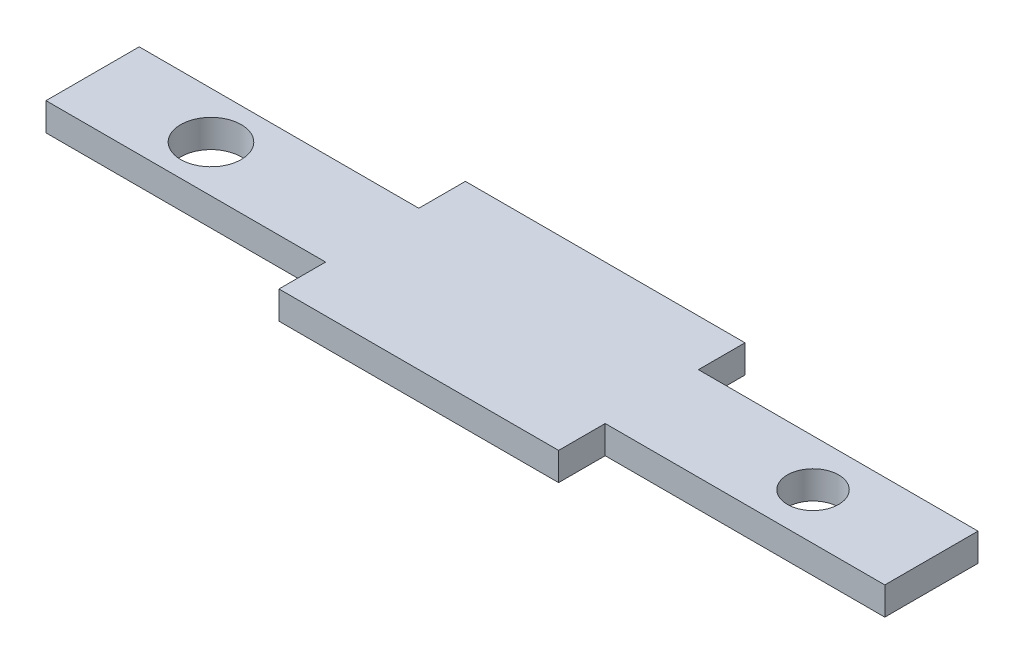
SolidWorks part; units mm, degrees
ref_plane "Front Plane" through (0, 0, 0) normal (0, 0, 1) x (1, 0, 0)
ref_plane "Top Plane" through (0, 0, 0) normal (0, 1, 0) x (1, 0, 0)
ref_plane "Right Plane" through (0, 0, 0) normal (1, 0, 0) x (0, 0, -1)
sketch "Sketch1" plane through (0, 0, 0) normal (0, 1, 0) x (1, 0, 0)
  line L0 (-32.4781, 0) -> (-32.4781, 10)
  line L1 (-32.4781, 10) -> (-2.4781, 10)
  line L2 (-2.4781, 10) -> (-2.4781, 15)
  line L3 (-2.4781, 15) -> (27.5219, 15)
  line L4 (27.5219, 15) -> (27.5219, 10)
  line L5 (27.5219, 10) -> (57.5219, 10)
  line L6 (57.5219, 10) -> (57.5219, 0)
  line L7 (57.5219, 0) -> (27.5219, 0)
  line L8 (27.5219, 0) -> (27.5219, -5)
  line L9 (27.5219, -5) -> (-2.4781, -5)
  line L10 (-2.4781, -5) -> (-2.4781, 0)
  line L11 (-2.4781, 0) -> (-32.4781, 0)
  line L12 (-32.4781, 5) -> (-19.7781, 5) construction
  line L13 (57.5219, 5) -> (44.8219, 5) construction
  circle A0 centre (-19.7781, 5) radius 3.25
  circle A1 centre (44.8219, 5) radius 2.75
  dimension "D5" = 6.5
  dimension "D6" = 5.5
  dimension "D1" = 5
  dimension "D2" = 10
  dimension "D3" = 30
  dimension "D4" = 30
extrude "Boss-Extrude1" add sketch "Sketch1" along normal blind 3
